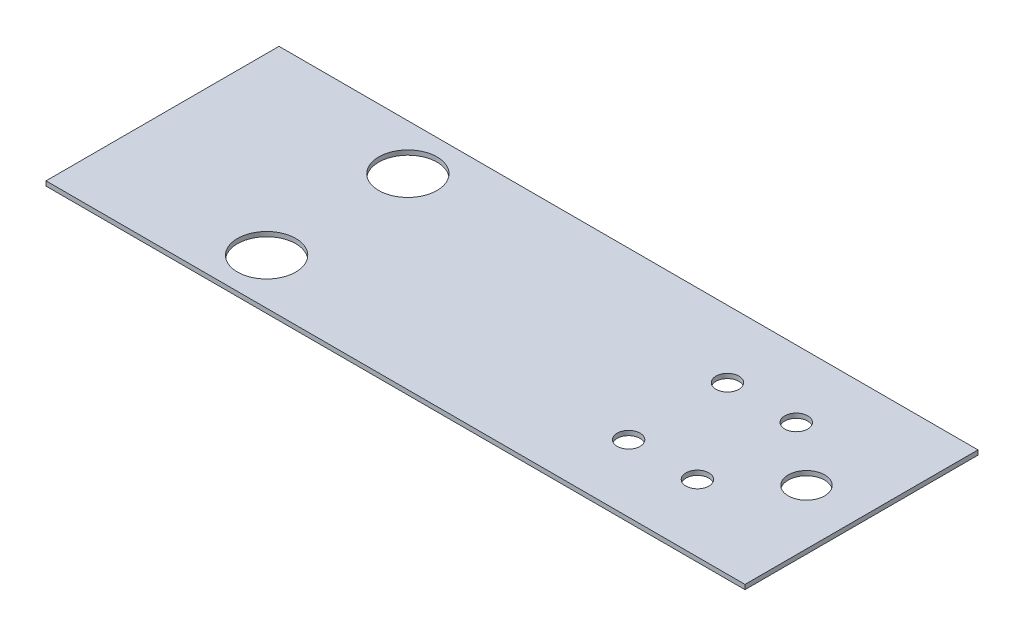
SolidWorks part; units mm, degrees
ref_plane "Plan de face" through (0, 0, 0) normal (0, 0, 1) x (1, 0, 0)
ref_plane "Plan de dessus" through (0, 0, 0) normal (0, 1, 0) x (1, 0, 0)
ref_plane "Plan de droite" through (0, 0, 0) normal (1, 0, 0) x (0, 0, -1)
sketch "Esquisse1" plane through (0, 0, 0) normal (0, 1, 0) x (1, 0, 0)
  line L1 (76.2, -25.4) -> (-76.2, -25.4)
  line L2 (76.2, -25.4) -> (76.2, 25.4)
  line L3 (76.2, 25.4) -> (-76.2, 25.4)
  line L4 (-76.2, -25.4) -> (-76.2, 25.4)
  line L5 (76.2, -25.4) -> (-76.2, 25.4) construction
  line L6 (76.2, 25.4) -> (-76.2, -25.4) construction
  point P0 (0, 0)
  dimension "D1" = 152.4
  dimension "D2" = 50.8
extrude "Boss.-Extru.1" add sketch "Esquisse1" along normal blind 1
sketch "Esquisse2" plane through (0, 1, 0) normal (0, 1, 0) x (1, 0, 0)
  line L1 (76.2, -25.4) -> (76.2, 25.4) construction
  line L2 (76.2, 25.4) -> (-76.2, 25.4) construction
  line L3 (-0.55, 0) -> (0.55, 0) construction
  circle A0 centre (-38.1, 15.4) radius 6.35
  circle A1 centre (-38.1, -15.4) radius 6.35
  dimension "D2" = 12.7
  dimension "D1" = 114.3
  dimension "D3" = 10
extrude "Enlèv. mat.-Extru.1" cut sketch "Esquisse2" against normal blind 1
sketch "Esquisse3" plane through (0, 1, 0) normal (0, 1, 0) x (1, 0, 0)
  line L0 (76.2, -25.4) -> (76.2, 25.4) construction
  line L1 (76.2, 25.4) -> (-76.2, 25.4) construction
  line L2 (-0.55, 0) -> (0.55, 0) construction
  circle A0 centre (51.2, 10.775) radius 2.5
  circle A1 centre (36.2, 10.775) radius 2.5
  circle A2 centre (36.2, -10.775) radius 2.5
  circle A3 centre (51.2, -10.775) radius 2.5
  point P8 (0, 0)
  dimension "D1" = 5
  dimension "D2" = 25
  dimension "D3" = 15
  dimension "D4" = 14.625
extrude "Enlèv. mat.-Extru.2" cut sketch "Esquisse3" against normal blind 1
sketch "Esquisse4" plane through (0, 1, 0) normal (0, 1, 0) x (1, 0, 0)
  line L0 (76.2, -25.4) -> (76.2, 25.4) construction
  circle A0 centre (64.2, 0) radius 3.9687
  point P6 (0, 0)
  dimension "D1" = 7.9375
  dimension "D2" = 12
extrude "Enlèv. mat.-Extru.3" cut sketch "Esquisse4" against normal blind 1
